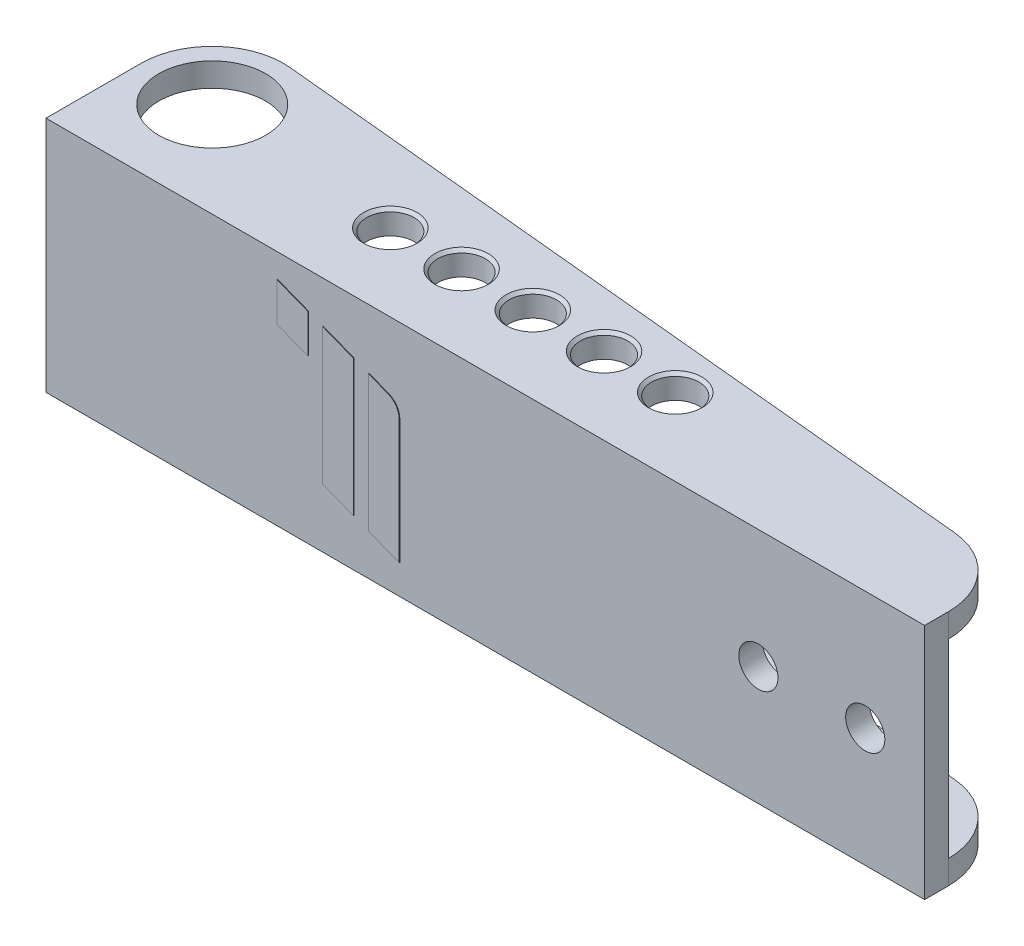
SolidWorks part; units mm, degrees
material "Alu 2017 (AU4G)"
ref_plane "Face" through (0, 0, 0) normal (0, 0, 1) x (1, 0, 0)
ref_plane "Dessus" through (0, 0, 0) normal (0, 1, 0) x (1, 0, 0)
ref_plane "Droite" through (0, 0, 0) normal (1, 0, 0) x (0, 0, -1)
sketch "Esquisse1" plane through (0, 0, 0) normal (0, 0, 1) x (1, 0, 0)
  line L1 (-74, 20) -> (74, 20)
  line L2 (-74, 20) -> (-74, -20)
  line L3 (-74, -20) -> (74, -20)
  line L4 (74, 20) -> (74, -20)
  line L5 (-74, 20) -> (74, -20) construction
  line L6 (-74, -20) -> (74, 20) construction
  point P0 (0, 0)
  dimension "D1" = 148
  dimension "D2" = 40
extrude "Boss.-Extru.1" add sketch "Esquisse1" along normal blind 30
sketch "Esquisse2" plane through (0, 20, 0) normal (0, 1, 0) x (1, 0, 0)
  line L0 (-74, -14) -> (-74, -30)
  line L1 (74, -30) -> (74, 0) construction
  line L2 (63.0503, -13.9489) -> (-60.8533, -2.0549)
  line L3 (-74, -30) -> (-74, 0) construction
  line L4 (-74, -30) -> (74, -30)
  line L5 (74, -26) -> (74, -30)
  arc A0 (-60.8533, -2.0549) -> (-74, -14) centre (-62, -14) ccw
  arc A1 (74, -26) -> (63.0503, -13.9489) centre (61.8935, -26) ccw
  point P17 (74, -15)
  point P18 (-62, -2)
  dimension "D1" = 16
  dimension "D2" = 28
  dimension "D3" = 4
extrude "Enlèv. mat.-Extru.1" cut sketch "Esquisse2" against normal through all flip side to cut
sketch "Esquisse3" plane through (-74, 0, 0) normal (-1, 0, 0) x (0, 0, 1)
  line L0 (2, 20) -> (2, -20) construction
  line L1 (2, 16) -> (26, 16)
  line L2 (2, 16) -> (2, -16)
  line L3 (2, -16) -> (26, -16)
  line L4 (26, 16) -> (26, -16)
  line L6 (0, 0) -> (26, 0) construction
  line L7 (30, 20) -> (30, -20) construction
  dimension "D1" = 32
  dimension "D2" = 4
extrude "Enlèv. mat.-Extru.3" cut sketch "Esquisse3" against normal through all
sketch "Esquisse4" plane through (0, 20, 0) normal (0, 1, 0) x (1, 0, 0)
  line L0 (74, -30) -> (-74, -30) construction
  line L1 (-74, -30) -> (-74, -14) construction
  circle A0 centre (-62, -14) radius 9
  circle A1 centre (-29, -17) radius 4
  circle A2 centre (-17, -17) radius 4
  circle A3 centre (-5, -17) radius 4
  circle A4 centre (7, -17) radius 4
  circle A5 centre (19, -17) radius 4
  dimension "D1" = 18
  dimension "D2" = 8
  dimension "D3" = 13
  dimension "D4" = 45
  dimension "D6" = 48
  dimension "D5" = 5
extrude "Enlèv. mat.-Extru.4" cut sketch "Esquisse4" against normal through all
chamfer "Chanfrein1" distance 0.5 angle 45 10 edges at (19, -20, 21) (7, -20, 21) (-5, -20, 21) (-17, -20, 21) (-29, -20, 21) (19, 20, 21) (7, 20, 21) (-5, 20, 21) (-17, 20, 21) (-29, 20, 21)
hole_wizard "Dégagement M61" positions "Esquisse8" profile "Esquisse7" hole size "M6" standard "ISO" end condition through all
sketch "Esquisse8" plane through (0, 0, 30) normal (0, 0, 1) x (1, 0, 0)
  line L0 (74, -20) -> (74, 20) construction
  point P0 (46, 0)
  point P2 (64, 0)
  dimension "D1" = 10
  dimension "D2" = 18
sketch "Esquisse7" plane through (46, 0, 30) normal (1, 0, 0) x (0, -1, 0)
  line L0 (0, 0) -> (0, 28)
  line L1 (0, 28) -> (3.3, 28)
  line L2 (3.3, 28) -> (3.3, 0)
  line L5 (3.3, 0) -> (0, 0)
  line L11 (0, -6.35) -> (0, 107.95) construction
  dimension "Diamètre du perçage jusqu'au prochain" = 6.6
  dimension "Profondeur du perçage jusqu'au prochain" = 28
sketch "Esquisse9" plane through (0, 0, 30) normal (0, 0, 1) x (1, 0, 0)
  line L0 (-35, 16) -> (-35, 9.5)
  line L1 (-35, 9.5) -> (-29.8, 7.474)
  line L2 (-29.8, 7.474) -> (-29.8, 13.974)
  line L3 (-29.8, 13.974) -> (-35, 16)
  line L4 (-27.3, 13) -> (-27.3, -9.974)
  line L5 (-27.3, -9.974) -> (-22.1, -12)
  line L6 (-22.1, -12) -> (-22.1, 10.974)
  line L7 (-22.1, 10.974) -> (-27.3, 13)
  line L8 (-19.6, 10) -> (-19.6, -12.974)
  line L9 (-19.6, -12.974) -> (-14.4, -15)
  line L10 (-14.4, -15) -> (-14.4, 5.9232)
  line L11 (-16.3109, 8.7185) -> (-19.6, 10)
  line L12 (74, 20) -> (-74, 20) construction
  line L13 (-74, -20) -> (74, -20) construction
  line L14 (-74, 20) -> (-74, -20) construction
  arc A0 (-14.4, 5.9232) -> (-16.3109, 8.7185) centre (-17.4, 5.9232) ccw
  dimension "D9" = 3
  dimension "D1" = 6.5
  dimension "D2" = 5.2
  dimension "D3" = 2.5
  dimension "D4" = 2.5
  dimension "D5" = 4
  dimension "D6" = 10
  dimension "D7" = 5
  dimension "D8" = 39
extrude "Boss.-Extru.2" add sketch "Esquisse9" along normal blind 0.1
